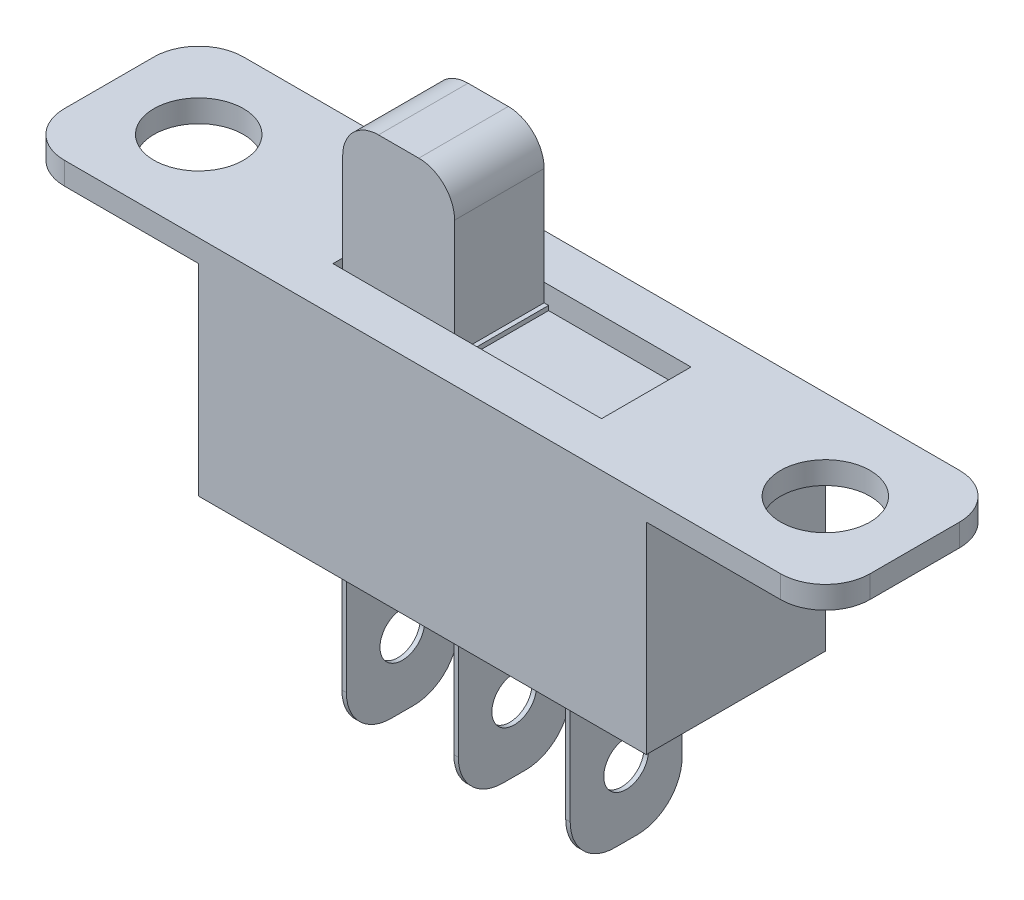
SolidWorks part; units mm, degrees
ref_plane "Front Plane" through (0, 0, 0) normal (0, 0, 1) x (1, 0, 0)
ref_plane "Top Plane" through (0, 0, 0) normal (0, 1, 0) x (1, 0, 0)
ref_plane "Right Plane" through (0, 0, 0) normal (1, 0, 0) x (0, 0, -1)
sketch "Sketch2" plane through (0, 0, 0) normal (0, 1, 0) x (1, 0, 0)
  line L1 (-5, 2) -> (5, 2)
  line L2 (-5, 2) -> (-5, -2)
  line L3 (-5, -2) -> (5, -2)
  line L4 (5, 2) -> (5, -2)
  line L5 (-5, 2) -> (5, -2) construction
  line L6 (-5, -2) -> (5, 2) construction
  point P0 (0, 0)
extrude "Boss-Extrude1" add sketch "Sketch2" along normal blind 5
sketch "Sketch3" plane through (0, 5, 0) normal (0, 1, 0) x (1, 0, 0)
  line L1 (-3, 1) -> (3, 1)
  line L2 (-3, 1) -> (-3, -1)
  line L3 (-3, -1) -> (3, -1)
  line L4 (3, 1) -> (3, -1)
  line L5 (-3, 1) -> (3, -1) construction
  line L6 (-3, -1) -> (3, 1) construction
  point P0 (0, 0)
extrude "Cut-Extrude1" cut sketch "Sketch3" against normal blind 0.5
sketch "Sketch4" plane through (5, 0, 0) normal (1, 0, 0) x (0, 0, -1)
  line L0 (2, 5) -> (2, 0) construction
  line L1 (-2, 5) -> (2, 5)
  line L2 (-2, 5) -> (-2, 4.5)
  line L3 (-2, 4.5) -> (2, 4.5)
  line L4 (2, 5) -> (2, 4.5)
extrude "Boss-Extrude2" add sketch "Sketch4" along normal blind 4
sketch "Sketch5" plane through (0, 4.5, 0) normal (0, -1, 0) x (1, 0, 0)
  circle A0 centre (7, 0) radius 1
extrude "Cut-Extrude2" cut sketch "Sketch5" against normal through all
mirror "Mirror3" about plane through (0, 0, 0) normal (1, 0, 0) of "Cut-Extrude2", "Boss-Extrude2"
fillet "Fillet1" radius 1 4 edges at (-9, 4.75, 2) (-9, 4.75, -2) (9, 4.75, -2) (9, 4.75, 2)
sketch "Sketch6" plane through (0, 4.5, 0) normal (0, 1, 0) x (1, 0, 0)
  line L0 (3, 1) -> (-3, 1) construction
  line L1 (-2.7825, 1) -> (-0.2825, 1)
  line L2 (-2.7825, 1) -> (-2.7825, -1)
  line L3 (-2.7825, -1) -> (-0.2825, -1)
  line L4 (-0.2825, 1) -> (-0.2825, -1)
  line L5 (-3, -1) -> (3, -1) construction
extrude "Boss-Extrude3" add sketch "Sketch6" along normal blind 3.5
fillet "Fillet2" radius 0.8 2 edges at (-2.7825, 8, 0) (-0.2825, 8, 0)
sketch "Sketch7" plane through (0, 4.5, 0) normal (0, 1, 0) x (1, 0, 0)
  line L0 (-0.2825, -1) -> (3, -1) construction
  line L1 (-0.2825, 1) -> (-0.1825, 1)
  line L2 (-0.2825, 1) -> (-0.2825, -1)
  line L3 (-0.2825, -1) -> (-0.1825, -1)
  line L4 (-0.1825, 1) -> (-0.1825, -1)
  line L5 (-3, -1) -> (-2.7825, -1) construction
  line L6 (-2.7825, 1) -> (-2.8825, 1)
  line L7 (-2.7825, 1) -> (-2.7825, -1)
  line L8 (-2.7825, -1) -> (-2.8825, -1)
  line L9 (-2.8825, 1) -> (-2.8825, -1)
extrude "Boss-Extrude4" add sketch "Sketch7" along normal blind 0.1
sketch "Sketch8" plane through (0, 0, 0) normal (0, -1, 0) x (1, 0, 0)
  line L1 (-4.85, 1.85) -> (4.85, 1.85)
  line L2 (-4.85, 1.85) -> (-4.85, -1.85)
  line L3 (-4.85, -1.85) -> (4.85, -1.85)
  line L4 (4.85, 1.85) -> (4.85, -1.85)
  line L5 (-4.85, 1.85) -> (4.85, -1.85) construction
  line L6 (-4.85, -1.85) -> (4.85, 1.85) construction
  point P0 (0, 0)
extrude "Cut-Extrude3" cut sketch "Sketch8" against normal blind 0.1
sketch "Sketch9" plane through (0, 0.1, 0) normal (0, -1, 0) x (1, 0, 0)
  line L0 (-6.796, 0) -> (7.4167, 0) construction
  line L3 (-0.05, 1.25) -> (0.05, 1.25)
  line L4 (-0.05, 1.25) -> (-0.05, -1.25)
  line L5 (-0.05, -1.25) -> (0.05, -1.25)
  line L6 (0.05, 1.25) -> (0.05, -1.25)
  line L7 (-0.05, 1.25) -> (0.05, -1.25) construction
  line L8 (-0.05, -1.25) -> (0.05, 1.25) construction
  point P3 (0, 0)
extrude "Boss-Extrude5" add sketch "Sketch9" along normal blind 4
fillet "Fillet3" radius 1 2 edges at (0, -3.9, -1.25) (0, -3.9, 1.25)
sketch "Sketch10" plane through (-0.05, 0, 0) normal (-1, 0, 0) x (0, 0, 1)
  line L0 (0.25, -3.9) -> (-0.25, -3.9) construction
  circle A0 centre (0, -2.4) radius 0.5
  point P4 (0, -3.9)
  dimension "D1" = 1.5
extrude "Cut-Extrude4" cut sketch "Sketch10" against normal through all
pattern_linear "LPattern1" count 2 spacing 2.5 along (1, 0, 0) count 2 spacing 2.5 along (-1, 0, 0) of "Cut-Extrude4", "Fillet3", "Boss-Extrude5"
